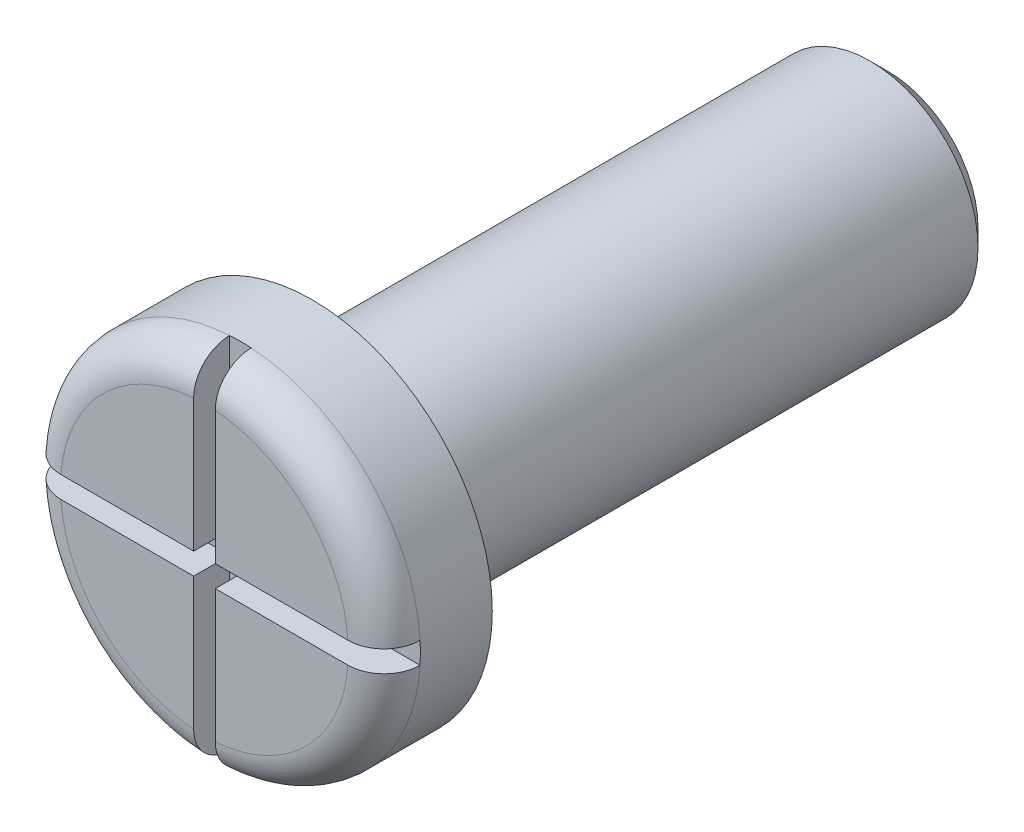
SolidWorks part; units mm, degrees
ref_plane "Front Plane" through (0, 0, 0) normal (0, 0, 1) x (1, 0, 0)
ref_plane "Top Plane" through (0, 0, 0) normal (0, 1, 0) x (1, 0, 0)
ref_plane "Right Plane" through (0, 0, 0) normal (1, 0, 0) x (0, 0, -1)
sketch "Sketch1" plane through (0, 0, 0) normal (1, 0, 0) x (0, 0, -1)
  line L0 (0, 0) -> (11.3738, 0) construction
  line L1 (9.5, 0) -> (9.5, 1.5)
  line L2 (9.5, 1.5) -> (1.5, 1.5)
  line L3 (1.5, 1.5) -> (1.5, 2.5)
  line L4 (1.5, 2.5) -> (0, 2.5)
  line L5 (0, 2.5) -> (0, 0)
  line L6 (0, 0) -> (9.5, 0)
  dimension "D1" = 8
  dimension "D2" = 1.5
  dimension "D3" = 5
  dimension "D4" = 1.5
revolve "Revolve1" add sketch "Sketch1" angle 360 about L0
sketch "Sketch2" plane through (0, 0, 0) normal (0, 0, 1) x (1, 0, 0)
  line L0 (0, 0) -> (3.0223, 0) construction
  line L1 (0, 0) -> (0, 3.0668) construction
  line L2 (-0.15, 2.4955) -> (-0.15, 0.15)
  line L3 (0.15, 2.4955) -> (0.15, 0.15)
  line L4 (-2.4955, 0.15) -> (-0.15, 0.15)
  line L5 (-2.4955, -0.15) -> (-0.15, -0.15)
  line L6 (0.15, 0.15) -> (2.4955, 0.15)
  line L7 (-0.15, -0.15) -> (-0.15, -2.4955)
  line L8 (0.15, -0.15) -> (2.4955, -0.15)
  line L9 (0.15, -0.15) -> (0.15, -2.4955)
  arc A1 (-2.4955, 0.15) -> (-2.4955, -0.15) centre (0, 0) ccw
  circle A2 centre (0, 0) radius 2.5 construction
  arc A3 (0.15, 2.4955) -> (-0.15, 2.4955) centre (0, 0) ccw
  arc A4 (2.4955, -0.15) -> (2.4955, 0.15) centre (0, 0) ccw
  arc A5 (-0.15, -2.4955) -> (0.15, -2.4955) centre (0, 0) ccw
  point P6 (0.15, 2.4955)
  point P8 (-2.4955, 0.15)
  point P11 (2.4955, 0.15)
  point P22 (0.15, -2.4955)
  dimension "D3" = 2.5
  dimension "D1" = 0.15
  dimension "D2" = 0.15
chamfer "Chamfer1" distance 0.25 angle 45 1 edges at (1.5, 0, -9.5)
extrude "Cut-Extrude1" cut sketch "Sketch2" against normal blind 0.5 contours L5 L7 A5 L9 L8 A4 L6 L3 A3 L2 L4 A1
fillet "Fillet7" radius 0.5 4 edges at (-1.7678, -1.7678, 0) (1.7678, -1.7678, 0) (1.7678, 1.7678, 0) (-1.7678, 1.7678, 0)
